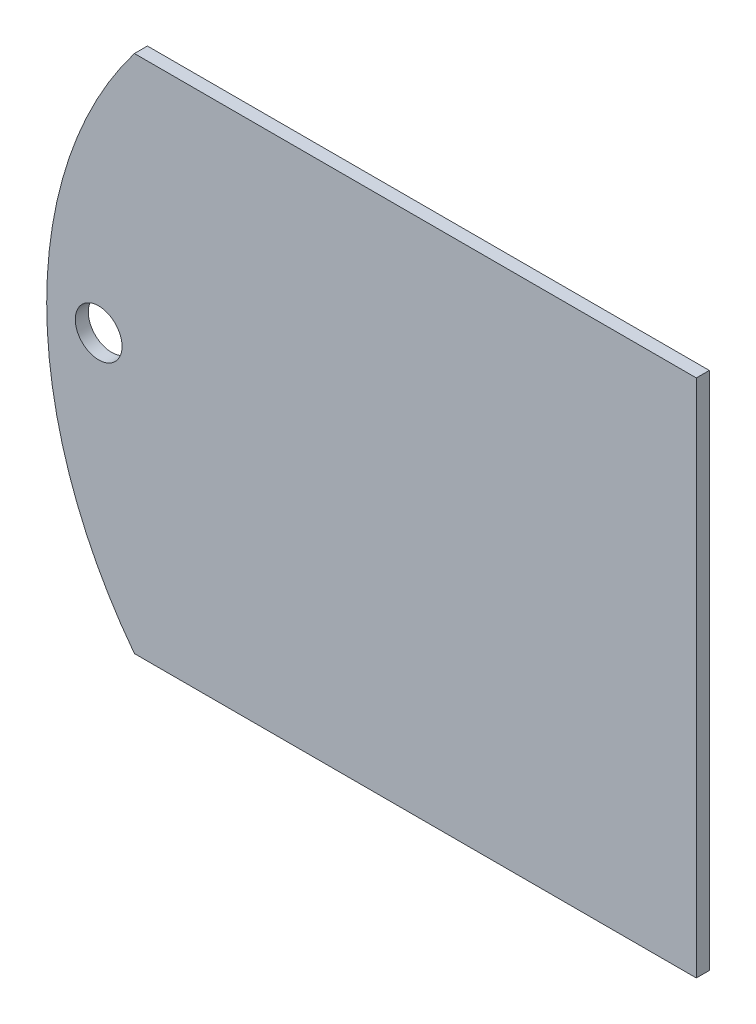
SolidWorks part; units mm, degrees
material "PEI"
ref_plane "Alzado" through (0, 0, 0) normal (0, 0, 1) x (1, 0, 0)
ref_plane "Planta" through (0, 0, 0) normal (0, 1, 0) x (1, 0, 0)
ref_plane "Vista lateral" through (0, 0, 0) normal (1, 0, 0) x (0, 0, -1)
sketch "Croquis1" plane through (0, 0, 0) normal (0, 0, 1) x (1, 0, 0)
  line L0 (-33, -20) -> (-33, 20) construction
  line L1 (0, 0) -> (0, 22.8374) construction
  line L2 (-26.2488, -20) -> (17, -20)
  line L3 (17, -20) -> (17, 20)
  line L4 (17, 20) -> (-33, 20)
  arc A0 (-26.2488, 20) -> (-26.2488, -20) centre (0, 0) ccw
  circle A1 centre (-29, 0) radius 1.8
  circle A2 centre (0, 0) radius 29 construction
  dimension "D1" = 66
  dimension "D5" = 4
  dimension "D6" = 3.6
  dimension "D2" = 20
  dimension "D3" = 20
  dimension "D4" = 50
extrude "Saliente-Extruir1" add sketch "Croquis1" along normal blind 1 contours L4 A0 L2 L3
